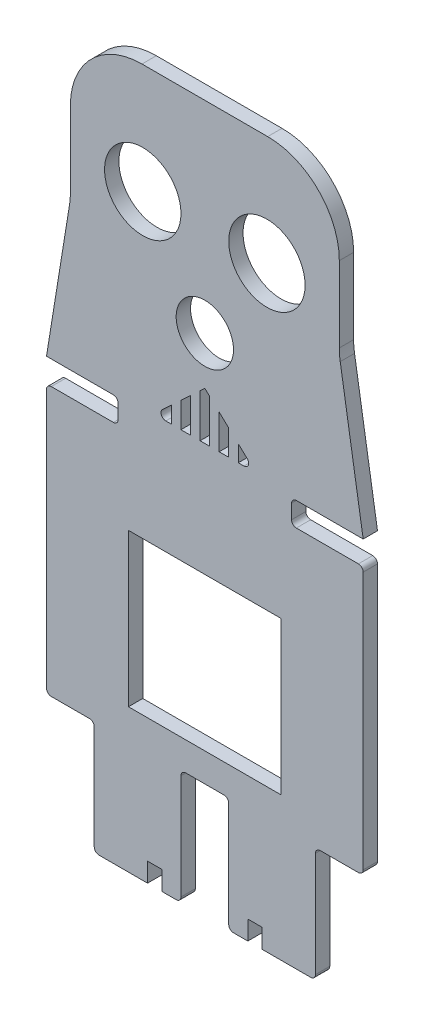
SolidWorks part; units mm, degrees
ref_plane "Alzado" through (0, 0, 0) normal (0, 0, 1) x (1, 0, 0)
ref_plane "Planta" through (0, 0, 0) normal (0, 1, 0) x (1, 0, 0)
ref_plane "Vista lateral" through (0, 0, 0) normal (1, 0, 0) x (0, 0, -1)
sketch "Model" plane through (0, 0, 0) normal (0, 0, 1) x (1, 0, 0)
  line L0 (4.3554, 22.4207) -> (5.5357, 22.4207)
  line L1 (4.3554, 25.8795) -> (4.3554, 22.4207)
  line L2 (6.1124, 24.2376) -> (4.3554, 25.8795)
  line L3 (2.3554, 22.4207) -> (0.3554, 22.4207)
  line L4 (2.3554, 27.7484) -> (2.3554, 22.4207)
  line L5 (0.3554, 29.6174) -> (2.3554, 27.7484)
  line L6 (0.3554, 22.4207) -> (0.3554, 29.6174)
  line L7 (-3.6446, 31.4863) -> (-2.6446, 32.4207)
  line L8 (-3.6446, 22.4207) -> (-3.6446, 31.4863)
  line L9 (-1.6446, 22.4207) -> (-3.6446, 22.4207)
  line L10 (-1.6446, 31.4863) -> (-1.6446, 22.4207)
  line L11 (-2.6446, 32.4207) -> (-1.6446, 31.4863)
  line L12 (-5.6446, 22.4207) -> (-7.6446, 22.4207)
  line L13 (-5.6446, 29.6174) -> (-5.6446, 22.4207)
  line L14 (-7.6446, 27.7484) -> (-5.6446, 29.6174)
  line L15 (-7.6446, 22.4207) -> (-7.6446, 27.7484)
  line L16 (-9.6446, 22.4207) -> (-10.8248, 22.4207)
  line L17 (-9.6446, 25.8795) -> (-9.6446, 22.4207)
  line L18 (-11.4016, 24.2376) -> (-9.6446, 25.8795)
  line L19 (30.519, 15.6722) -> (30.519, -38.3278)
  line L20 (-21.8082, 16.6722) -> (-34.8082, 16.6722)
  line L21 (-20.8082, 20.6722) -> (-20.8082, 17.6722)
  line L22 (-35.8082, 21.6722) -> (-21.8082, 21.6722)
  line L23 (16.519, 16.6722) -> (29.519, 16.6722)
  line L24 (15.519, 20.6722) -> (15.519, 17.6722)
  line L25 (30.519, 21.6722) -> (16.519, 21.6722)
  line L26 (25.7108, 51.4494) -> (30.519, 21.6722)
  line L27 (25.519, 62.4713) -> (25.519, 53.8405)
  line L28 (-31, 51.4494) -> (-35.8082, 21.6722)
  line L29 (25.519, 69.6722) -> (25.519, 62.4713)
  line L30 (-6.6446, -39.3278) -> (1.3554, -39.3278)
  line L31 (-7.6446, -62.3278) -> (-7.6446, -40.3278)
  line L32 (-11.6446, -63.3278) -> (-8.6446, -63.3278)
  line L33 (-11.6446, -59.3278) -> (-11.6446, -63.3278)
  line L34 (-14.6446, -59.3278) -> (-11.6446, -59.3278)
  line L35 (-14.6446, -63.3278) -> (-14.6446, -59.3278)
  line L36 (-24.8082, -63.3278) -> (-14.6446, -63.3278)
  line L37 (-25.8082, -40.5496) -> (-25.8082, -62.3278)
  line L38 (-34.8082, -39.5496) -> (-26.8082, -39.5496)
  line L39 (-35.8082, 8.9785) -> (-35.8082, -38.5496)
  line L40 (21.519, -39.3278) -> (29.519, -39.3278)
  line L41 (20.519, -62.3278) -> (20.519, -40.3278)
  line L42 (9.3554, -63.3278) -> (19.519, -63.3278)
  line L43 (9.3554, -59.3278) -> (9.3554, -63.3278)
  line L44 (6.3554, -59.3278) -> (9.3554, -59.3278)
  line L45 (6.3554, -63.3278) -> (6.3554, -59.3278)
  line L46 (3.3554, -63.3278) -> (6.3554, -63.3278)
  line L47 (2.3554, -40.3278) -> (2.3554, -62.3278)
  line L48 (-35.8082, 15.6722) -> (-35.8082, 8.9785)
  line L49 (-15.8082, 84.6722) -> (10.519, 84.6722)
  line L50 (-30.8082, 53.8405) -> (-30.8082, 69.6722)
  line L51 (13.3554, -33.3278) -> (-18.6446, -33.3278)
  line L52 (13.3554, -1.3278) -> (13.3554, -33.3278)
  line L53 (-2.1446, -1.3278) -> (13.3554, -1.3278)
  line L54 (-18.6446, -1.3278) -> (-2.1446, -1.3278)
  line L55 (-18.6446, -33.3278) -> (-18.6446, -1.3278)
  arc A0 (5.5357, 22.4207) -> (6.1124, 24.2376) centre (5.5357, 23.4207) ccw
  arc A1 (-11.4016, 24.2376) -> (-10.8248, 22.4207) centre (-10.8248, 23.4207) ccw
  arc A2 (-34.8082, 16.6722) -> (-35.8082, 15.6722) centre (-34.8082, 15.6722) ccw
  arc A3 (-21.8082, 16.6722) -> (-20.8082, 17.6722) centre (-21.8082, 17.6722) ccw
  arc A4 (-20.8082, 20.6722) -> (-21.8082, 21.6722) centre (-21.8082, 20.6722) ccw
  arc A5 (30.519, 15.6722) -> (29.519, 16.6722) centre (29.519, 15.6722) ccw
  arc A6 (15.519, 17.6722) -> (16.519, 16.6722) centre (16.519, 17.6722) ccw
  arc A7 (16.519, 21.6722) -> (15.519, 20.6722) centre (16.519, 20.6722) ccw
  arc A8 (2.3554, -40.3278) -> (1.3554, -39.3278) centre (1.3554, -40.3278) ccw
  arc A9 (-6.6446, -39.3278) -> (-7.6446, -40.3278) centre (-6.6446, -40.3278) ccw
  arc A10 (-8.6446, -63.3278) -> (-7.6446, -62.3278) centre (-8.6446, -62.3278) ccw
  arc A11 (-25.8082, -62.3278) -> (-24.8082, -63.3278) centre (-24.8082, -62.3278) ccw
  arc A12 (-25.8082, -40.5496) -> (-26.8082, -39.5496) centre (-26.8082, -40.5496) ccw
  arc A13 (-35.8082, -38.5496) -> (-34.8082, -39.5496) centre (-34.8082, -38.5496) ccw
  arc A14 (29.519, -39.3278) -> (30.519, -38.3278) centre (29.519, -38.3278) ccw
  arc A15 (21.519, -39.3278) -> (20.519, -40.3278) centre (21.519, -40.3278) ccw
  arc A16 (19.519, -63.3278) -> (20.519, -62.3278) centre (19.519, -62.3278) ccw
  arc A17 (2.3554, -62.3278) -> (3.3554, -63.3278) centre (3.3554, -62.3278) ccw
  arc A18 (25.519, 69.6722) -> (10.519, 84.6722) centre (10.519, 69.6722) ccw
  arc A19 (-15.8082, 84.6722) -> (-30.8082, 69.6722) centre (-15.8082, 69.6722) ccw
  arc A20 (-31, 51.4494) -> (-30.8082, 53.8405) centre (-45.8082, 53.8405) ccw
  arc A21 (25.519, 53.8405) -> (25.7108, 51.4494) centre (40.519, 53.8405) ccw
  circle A22 centre (-15.6446, 61.6207) radius 8
  circle A23 centre (10.3554, 61.6207) radius 8
  circle A24 centre (-2.6446, 42.4207) radius 6
extrude "Saliente-Extruir1" add sketch "Model" along normal blind 3
